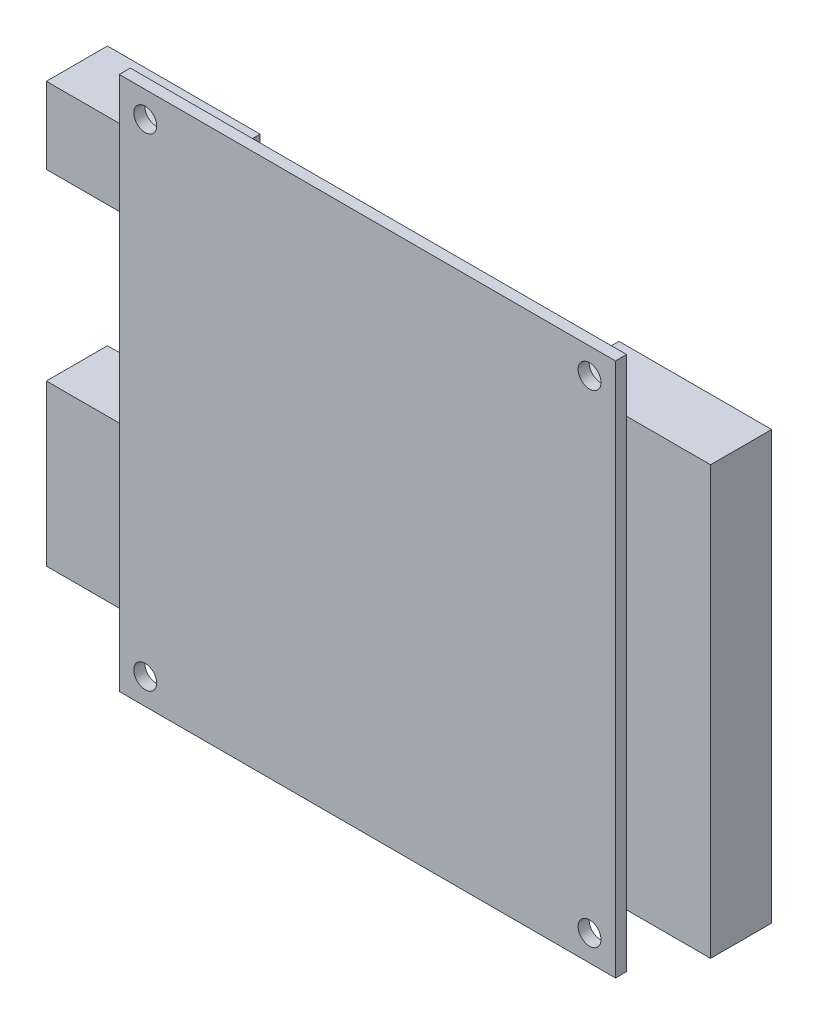
SolidWorks part; units mm, degrees
ref_plane "前基準面" through (0, 0, 0) normal (0, 0, 1) x (1, 0, 0)
ref_plane "上基準面" through (0, 0, 0) normal (0, 1, 0) x (1, 0, 0)
ref_plane "右基準面" through (0, 0, 0) normal (1, 0, 0) x (0, 0, -1)
sketch "草圖1" plane through (0, 0, 0) normal (0, 0, 1) x (1, 0, 0)
  line L1 (-32.5, 35) -> (32.5, 35)
  line L2 (-32.5, 35) -> (-32.5, -35)
  line L3 (-32.5, -35) -> (32.5, -35)
  line L4 (32.5, 35) -> (32.5, -35)
  line L5 (-32.5, 35) -> (32.5, -35) construction
  line L6 (-32.5, -35) -> (32.5, 35) construction
  point P0 (0, 0)
  dimension "D1" = 65
  dimension "D2" = 70
extrude "填料-伸長1" add sketch "草圖1" along normal blind 1.45
sketch "草圖2" plane through (0, 0, 0) normal (0, 0, -1) x (-1, 0, 0)
  line L0 (32.5, 35) -> (32.5, -35) construction
  line L1 (-32.5, 35) -> (32.5, 35) construction
  circle A0 centre (29.1, 31.6) radius 1.5
  dimension "D3" = 3
  dimension "D1" = 3.4
  dimension "D2" = 3.4
extrude "除料-伸長1" cut sketch "草圖2" against normal through all
mirror "鏡射1" about plane through (0, 0, 0) normal (1, 0, 0) of "除料-伸長1"
mirror "鏡射2" about plane through (0, 0, 0) normal (0, 1, 0) of "鏡射1", "除料-伸長1"
sketch "草圖3" plane through (0, 0, 0) normal (0, 0, -1) x (-1, 0, 0)
  line L1 (-33.5, 28) -> (-23.5, 28)
  line L2 (-33.5, 28) -> (-33.5, -28)
  line L3 (-33.5, -28) -> (-23.5, -28)
  line L4 (-23.5, 28) -> (-23.5, -28)
  line L5 (-32.5, 35) -> (32.5, 35) construction
  line L6 (32.5, -35) -> (-32.5, -35) construction
  line L7 (32.5, 35) -> (32.5, -35) construction
  dimension "D1" = 7
  dimension "D2" = 7
  dimension "D3" = 10
  dimension "D4" = 56
extrude "填料-伸長3" add sketch "草圖3" along normal blind 8
sketch "草圖4" plane through (0, 0, 0) normal (0, 0, -1) x (-1, 0, 0)
  line L0 (-32.5, 28) -> (-32.5, 35) construction
  line L1 (23.5, 28) -> (33.5, 28)
  line L2 (23.5, 28) -> (23.5, 18)
  line L3 (23.5, 18) -> (33.5, 18)
  line L4 (33.5, 28) -> (33.5, 18)
  line L5 (-32.5, 35) -> (32.5, 35) construction
  dimension "D1" = 10
  dimension "D2" = 56
  dimension "D3" = 10
  dimension "D4" = 7
extrude "填料-伸長4" add sketch "草圖4" along normal blind 8
sketch "草圖5" plane through (0, 0, 0) normal (0, 0, -1) x (-1, 0, 0)
  line L0 (23.5, 18) -> (32.5, 18) construction
  line L1 (23.5, 17) -> (33.5, 17)
  line L2 (23.5, 17) -> (23.5, -5)
  line L3 (23.5, -5) -> (33.5, -5)
  line L4 (33.5, 17) -> (33.5, -5)
  line L5 (-33.5, 28) -> (-33.5, -28) construction
  dimension "D1" = 10
  dimension "D2" = 22
  dimension "D3" = 1
  dimension "D4" = 57
extrude "填料-伸長5" add sketch "草圖5" along normal blind 8
sketch "草圖6" plane through (0, 0, 0) normal (0, 0, -1) x (-1, 0, 0)
  line L0 (23.5, -5) -> (32.5, -5) construction
  line L1 (23.5, -6) -> (33.5, -6)
  line L2 (23.5, -6) -> (23.5, -27)
  line L3 (23.5, -27) -> (33.5, -27)
  line L4 (33.5, -6) -> (33.5, -27)
  line L5 (-32.5, -35) -> (-32.5, -28) construction
  dimension "D1" = 10
  dimension "D2" = 21
  dimension "D3" = 1
  dimension "D4" = 56
extrude "填料-伸長6" add sketch "草圖6" along normal blind 8
sketch "草圖7" plane through (-33.5, 0, 0) normal (-1, 0, 0) x (0, 0, 1)
  line L0 (0, -27) -> (0, -6) construction
  line L1 (-8, -27) -> (0, -27)
  line L2 (-8, -27) -> (-8, -6)
  line L3 (-8, -6) -> (0, -6)
  line L4 (0, -27) -> (0, -6)
extrude "填料-伸長7" add sketch "草圖7" along normal blind 10
sketch "草圖9" plane through (-33.5, 0, 0) normal (-1, 0, 0) x (0, 0, 1)
  line L1 (-8, 18) -> (0, 18)
  line L2 (-8, 18) -> (-8, 28)
  line L3 (-8, 28) -> (0, 28)
  line L4 (0, 18) -> (0, 28)
extrude "填料-伸長9" add sketch "草圖9" along normal blind 10
sketch "草圖10" plane through (33.5, 0, 0) normal (1, 0, 0) x (0, 0, -1)
  line L1 (8, 28) -> (0, 28)
  line L2 (8, 28) -> (8, -28)
  line L3 (8, -28) -> (0, -28)
  line L4 (0, 28) -> (0, -28)
extrude "填料-伸長10" add sketch "草圖10" along normal blind 10
